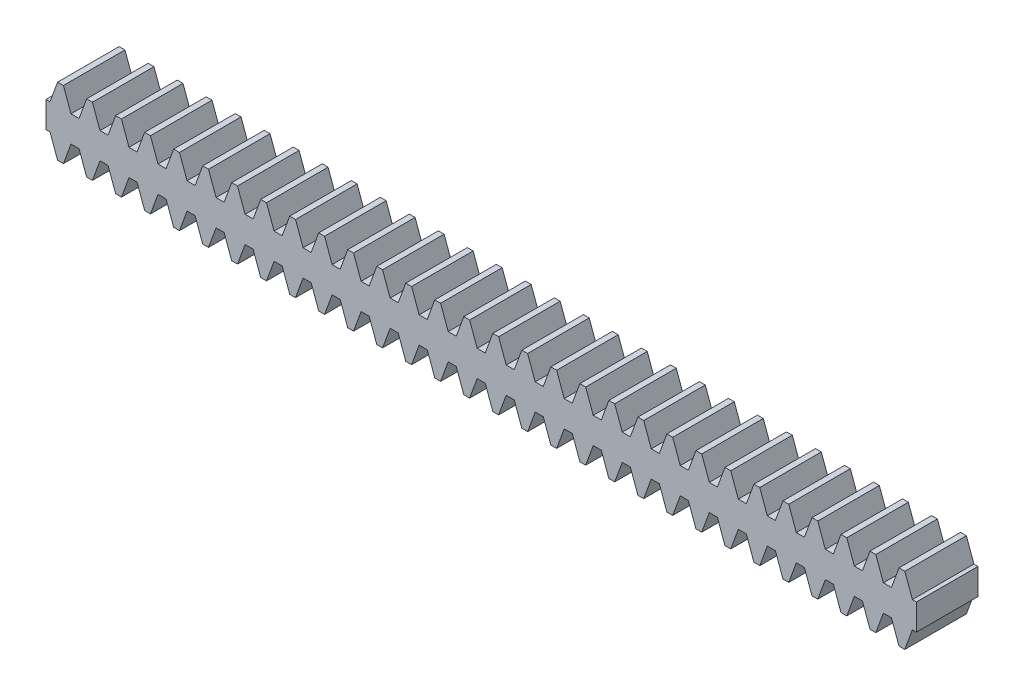
SolidWorks part; units mm, degrees
extrude "Blank" add sketch "BlankSke" against normal blind 10
sketch "BlankSke" plane through (0, 0, 0) normal (0, 0, 1) x (1, 0, 0)
  line L1 (0, 0) -> (200, 0)
  line L2 (0, 0) -> (0, 5.5)
  line L3 (0, 5.5) -> (200, 5.5)
  line L4 (200, 0) -> (200, 5.5)
  dimension "Length" = 200
  dimension "Blank_height" = 5.5
ref_plane "Plane1" through (0, 0, 0) normal (0, 0, 1) x (1, 0, 0)
ref_plane "Plane2" through (0, 0, 0) normal (0, 1, 0) x (1, 0, 0)
ref_plane "Plane3" through (0, 0, 0) normal (1, 0, 0) x (0, 0, -1)
sketch "HoldingSke" plane through (0, 0, 0) normal (0, 1, 0) x (1, 0, 0)
  line L0 (0, 0) -> (0.0928, 0.6602)
  line L1 (-15, 0) -> (100, 0) construction
  line L2 (0, 0) -> (-2.1039, 2.3779)
  line L3 (0, 0) -> (-11.863, 4.5341)
  line L4 (0, 0) -> (6.2122, 5.9991)
  line L5 (0, 0) -> (-23.7986, -8.8762)
  line L6 (0, 0) -> (-10.5278, -7.1032)
  line L9 (-71.009, 38.7566) -> (116.9296, 107.1606)
  line L10 (-76.2, 3.8779) -> (-72.2, 3.8779)
  line L11 (0, 0) -> (-10, 0)
  line L12 (-76.2, 101.6) -> (-76.147, 101.6)
  line L13 (24.9733, 27.94) -> (52.9518, 28.4284)
  line L14 (24.9733, 27.94) -> (24.9743, 27.94)
  line L15 (24.9733, 27.94) -> (100.4006, 29.5858)
  circle A0 centre (0, 0) radius 19.05
  circle A1 centre (0, 0) radius 2
  circle A2 centre (0, 0) radius 12.7
  dimension "MPH" = 4
  dimension "Diameter" = 38.1
  dimension "Num_teeth" = 44
  dimension "Pitch" = 0.6667
  dimension "Show_teeth" = 998
  dimension "Thickness" = 12.7
  dimension "Ap" = 20
  dimension "Pitch_height" = 4
  dimension "Width" = 10
  dimension "Backlash" = 0.053
  dimension "Addendum_fac" = 1
  dimension "Dedendum_fac" = 1.25
  dimension "Clearance_fac" = 0.25
  dimension "Dedendum_add" = 0.001
  dimension "Length" = 200
  dimension "Module" = 1.5
sketch "TooCutSkeIll" plane through (0, 0, 0) normal (0, 0, 1) x (1, 0, 0)
  line L0 (-1.8687, 5.4605) -> (-0.7447, 2.3724)
  line L1 (-0.3914, 2.125) -> (0.3914, 2.125)
  line L2 (0.7447, 2.3724) -> (1.8687, 5.4605)
  line L3 (200, 5.5) -> (0, 5.5) construction
  line L4 (0, 0) -> (0, 64.897) construction
  line L5 (-13.208, 4) -> (12.954, 4) construction
  line L6 (0, 0) -> (200, 0) construction
  line L7 (1.3371, 4) -> (1.3371, 48.7463) construction
  line L8 (-1.3371, 4) -> (-1.3371, 48.7463) construction
  line L9 (1.9251, 5.5) -> (1.9251, 5.5254)
  line L10 (-1.9251, 5.5) -> (-1.9251, 5.5254)
  line L11 (-1.9251, 5.5254) -> (1.9251, 5.5254)
  arc A0 (0.3914, 2.125) -> (0.7447, 2.3724) centre (0.3914, 2.501) ccw
  arc A1 (-0.7447, 2.3724) -> (-0.3914, 2.125) centre (-0.3914, 2.501) ccw
  arc A2 (1.9251, 5.5) -> (1.8687, 5.4605) centre (1.9251, 5.44) ccw
  arc A3 (-1.8687, 5.4605) -> (-1.9251, 5.5) centre (-1.9251, 5.44) ccw
  dimension "Pitch_height" = 4
  dimension "Addendum_plus" = 1.5254
  dimension "Pressure_angle" = 20
  dimension "Gap_width" = 2.6742
  dimension "Dedendum" = 1.875
extrude "ToothCutIll" [suppressed] cut sketch "TooCutSkeIll" against normal through all
sketch "TooCutSkeSim" plane through (0, 0, 0) normal (0, 0, 1) x (1, 0, 0)
  line L0 (0.6547, 2.125) -> (-0.6547, 2.125)
  line L1 (1.8923, 5.5254) -> (0.6547, 2.125)
  line L2 (0, 17.4625) -> (0, 53.467) construction
  line L3 (1.8923, 5.5254) -> (-1.8923, 5.5254)
  line L6 (-1.8923, 5.5254) -> (-0.6547, 2.125)
  line L9 (-1.3371, 4) -> (1.3371, 4) construction
  line L10 (0, 0) -> (200, 0) construction
  line L11 (1.3371, 4) -> (1.3371, 53.467) construction
  line L12 (-1.3371, 4) -> (-1.3371, 53.467) construction
  dimension "Pitch_height" = 4
  dimension "Addendum_plus" = 1.5254
  dimension "Pressure_angle" = 20
  dimension "Gap_width" = 2.6742
  dimension "Dedendum" = 1.875
extrude "ToothCutSim" cut sketch "TooCutSkeSim" against normal through all
pattern_linear "TeethCuts" count 43 spacing 4.7124 along (1, 0, 0) of "ToothCutIll", "ToothCutSim"
mirror "Mirror1" about plane through (0, 0, -10) normal (0, -1, 0) of bodies 102
sketch "Sketch1" plane through (0, 0, -10) normal (0, 0, -1) x (-1, 0, 0)
  line L0 (-200, 0) -> (0, 0)
  line L1 (-200, -5.5) -> (-200, 5.5) construction
  line L2 (0, 2.125) -> (0, -2.125) construction
sketch "Sketch2" plane through (0, 0, 0) normal (0, 0, 1) x (1, 0, 0)
  line L1 (141.3742, 17.0427) -> (204.6993, 17.0427)
  line L2 (141.3742, 17.0427) -> (141.3742, -10.5212)
  line L3 (141.3742, -10.5212) -> (204.6993, -10.5212)
  line L4 (204.6993, 17.0427) -> (204.6993, -10.5212)
extrude "Cut-Extrude1" cut sketch "Sketch2" against normal blind 10
equation "' \"Module@HoldingSke\" = 6.35"
equation "' \"Num_teeth@HoldingSke\" = 12"
equation "' \"Ap@HoldingSke\" =  20"
equation "' \"Ap@HoldingSke\" = 20"
equation "' \"Width@HoldingSke\" = 0.25 * 25.4"
equation "' \"Show_teeth@HoldingSke\" = 500"
equation "' \"Backlash@HoldingSke\" = 0.009 * 25.4"
equation "' \"Addendum_fac@HoldingSke\" = 1.0"
equation "' \"Dedendum_fac@HoldingSke\" = 1.25"
equation "' \"Dedendum_add@HoldingSke\" = 0.00005 * 25.4"
equation "' \"Clearance_fac@HoldingSke\" = 0.25"
equation "' \"Pitch_height@HoldingSke\" = 1 * 25.4"
equation "' \"Length@HoldingSke\" = 4.71 * 25.4"
equation "\"Pitch@HoldingSke\" = 1 / \"Module@HoldingSke\""
equation "\"MPH@HoldingSke\" = \"Dedendum_fac@HoldingSke\" / \"Pitch@HoldingSke\" + 2 * \"Dedendum_add@HoldingSke\" + 0.002 * 25.4"
equation "\"MPH@HoldingSke\" = ((sgn( \"MPH@HoldingSke\" - \"Pitch_height@HoldingSke\")+1)*( \"MPH@HoldingSke\" - \"Pitch_height@HoldingSke\"))/2 + \"Pitch_height@HoldingSke\""
equation "\"Blank_height@BlankSke\" = \"Pitch_height@HoldingSke\" + \"Addendum_fac@HoldingSke\"  / \"Pitch@HoldingSke\" "
equation "\"Length@BlankSke\" =  \"Length@HoldingSke\""
equation "\"Face_width@Blank\" = \"Width@HoldingSke\""
equation "\"Pressure_angle@TooCutSkeIll\" = \"Ap@HoldingSke\""
equation "\"Addendum_plus@TooCutSkeIll\" =  \"Addendum_fac@HoldingSke\"  / \"Pitch@HoldingSke\" + 0.001 *25.4"
equation "\"Dedendum@TooCutSkeIll\" = \"Dedendum_fac@HoldingSke\"  / \"Pitch@HoldingSke\""
equation "\"Pitch_height@TooCutSkeIll\" =  \"MPH@HoldingSke\""
equation "\"Gap_width@TooCutSkeIll\" = 3.14159265 / 2 / \"Pitch@HoldingSke\" + 6 * \"Backlash@HoldingSke\""
equation "\"Pressure_angle@TooCutSkeSim\" = \"Ap@HoldingSke\""
equation "\"Addendum_plus@TooCutSkeSim\" =  \"Addendum_fac@HoldingSke\"  / \"Pitch@HoldingSke\" + 0.001 * 25.4"
equation "\"Dedendum@TooCutSkeSim\" = \"Dedendum_fac@HoldingSke\"  / \"Pitch@HoldingSke\""
equation "\"Pitch_height@TooCutSkeSim\" =  \"MPH@HoldingSke\""
equation "\"Gap_width@TooCutSkeSim\" = 3.14159265 / 2 / \"Pitch@HoldingSke\" + 6 * \"Backlash@HoldingSke\""
equation "\"Root_fillet@TooCutSkeIll\" = \"Clearance_fac@HoldingSke\" / \"Pitch@HoldingSke\" + \"Dedendum_add@HoldingSke\""
equation "\"Break_rad@TooCutSkeIll\" = 0.02 / \"Pitch@HoldingSke\" * 2"
equation "\"Linear_pitch@TeethCuts\" = 3.14159265 / \"Pitch@HoldingSke\""
equation "\"Num_teeth@HoldingSke\" = int( ( \"Length@HoldingSke\" + 0 ) / (3.14159265 / \"Pitch@HoldingSke\")) + 0.9999  + 1"
equation " \"Num_teeth@TeethCuts\" = int( \"Show_teeth@HoldingSke\" ) + 1"
equation " \"Num_teeth@TeethCuts\" = ((sgn( \"Num_teeth@TeethCuts\" - \"Num_teeth@HoldingSke\" )-1)*( \"Num_teeth@TeethCuts\" - \"Num_teeth@HoldingSke\" ))/-2+ \"Num_teeth@HoldingSke\""
equation " \"Num_teeth@TeethCuts\" = ((sgn( \"Num_teeth@TeethCuts\" - 2.0)+1)*( \"Num_teeth@TeethCuts\" - 2.0))/2 +2.0"
